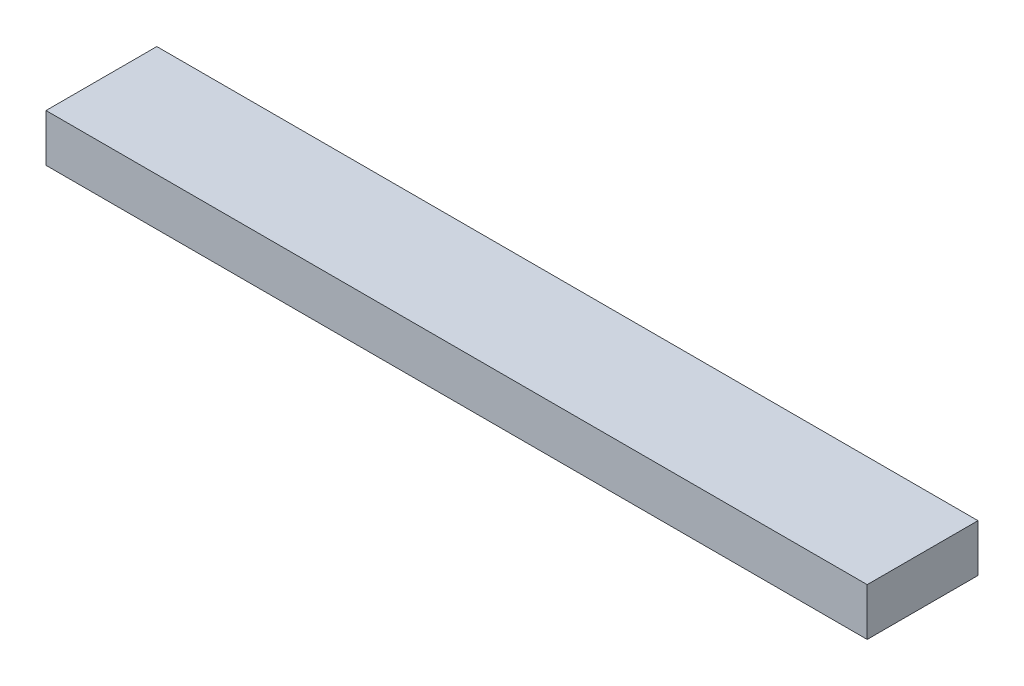
SolidWorks part; units mm, degrees
material "Pine"
ref_plane "Front Plane" through (0, 0, 0) normal (0, 0, 1) x (1, 0, 0)
ref_plane "Top Plane" through (0, 0, 0) normal (0, 1, 0) x (1, 0, 0)
ref_plane "Right Plane" through (0, 0, 0) normal (1, 0, 0) x (0, 0, -1)
sketch "Sketch1" plane through (0, 0, 0) normal (0, 1, 0) x (1, 0, 0)
  line L1 (0, 0) -> (658.8125, 0)
  line L2 (0, 0) -> (0, 88.9)
  line L3 (0, 88.9) -> (658.8125, 88.9)
  line L4 (658.8125, 0) -> (658.8125, 88.9)
  dimension "D1" = 88.9
  dimension "D2" = 658.8125
extrude "Boss-Extrude1" add sketch "Sketch1" along normal blind 38.1
